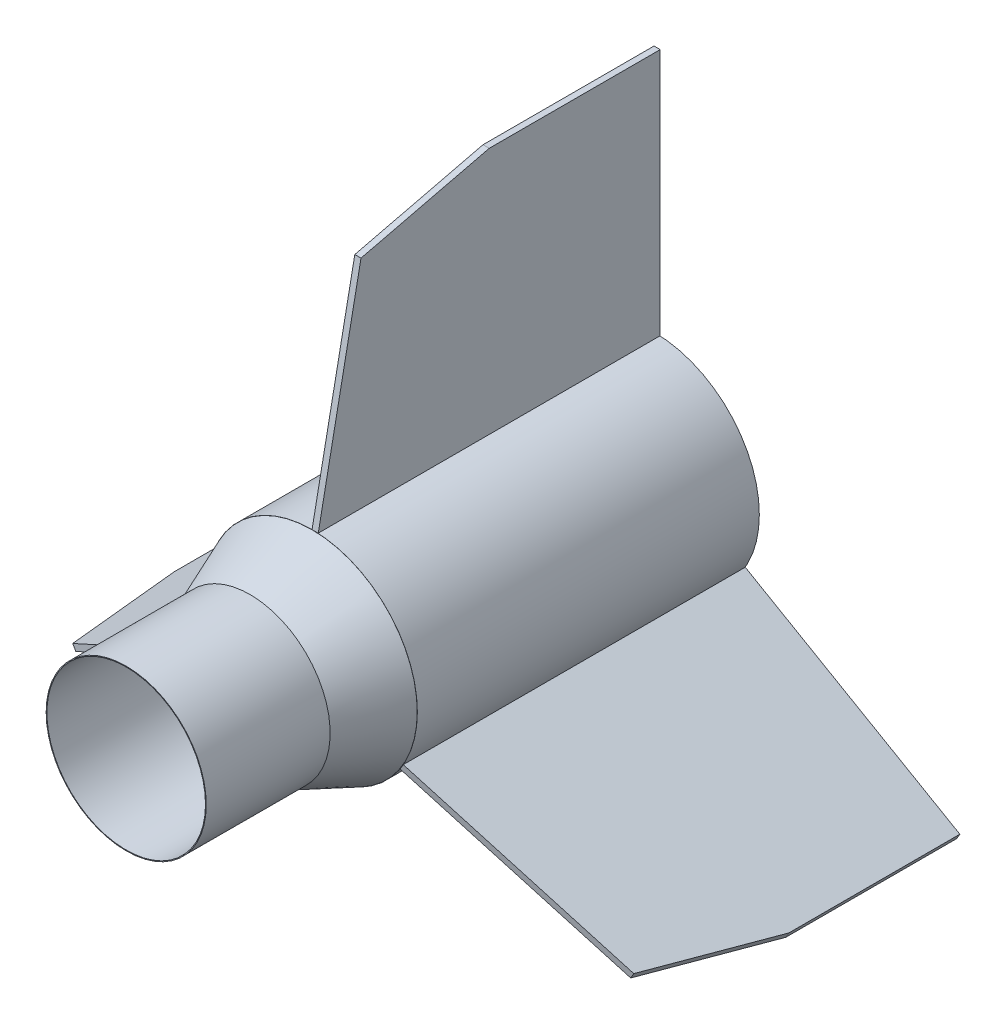
SolidWorks part; units mm, degrees
ref_plane "Front Plane" through (0, 0, 0) normal (0, 0, 1) x (1, 0, 0)
ref_plane "Top Plane" through (0, 0, 0) normal (0, 1, 0) x (1, 0, 0)
ref_plane "Right Plane" through (0, 0, 0) normal (1, 0, 0) x (0, 0, -1)
sketch "Sketch1" plane through (0, 0, 0) normal (0, 0, 1) x (1, 0, 0)
  line L0 (0, 0) -> (-20.1218, 11.3741) construction
  line L1 (0, 0) -> (19.9112, 11.7389) construction
  line L2 (0, 0) -> (0.2377, -23.114) construction
  circle A4 centre (0.1189, -11.557) radius 9.144
  circle A5 centre (9.9556, 5.8695) radius 9.144
  circle A6 centre (-10.0609, 5.687) radius 9.144
  circle A8 centre (0, 0) radius 21.59
  point P1 (2.188, 1.29)
  point P2 (-2.2112, 1.2499)
  point P6 (0.0261, -2.54)
  point P7 (9.9556, 5.8695)
  point P8 (-10.0609, 5.687)
  point P9 (0.1189, -11.557)
  dimension "D1" = 2.54
  dimension "D2" = 2.54
  dimension "D3" = 2.54
  dimension "D4" = 9.017
  dimension "D5" = 9.017
  dimension "D6" = 9.017
extrude "Boss-Extrude1" add sketch "Sketch1" along normal blind 70.1
sketch "Sketch2" plane through (0, 0, 70.1) normal (0, 0, 1) x (1, 0, 0)
  circle A0 centre (0, 0) radius 21.59
  circle A2 centre (0, 0) radius 16.4084
  circle A3 centre (0, 0) radius 16.256
  circle M4 centre (9.9556, 5.8695) radius 9.144
  circle M6 centre (0.1189, -11.557) radius 9.144
  circle M7 centre (-10.0609, 5.687) radius 9.144
extrude "Boss-Extrude2" add sketch "Sketch2" along normal blind 38.1 contours A3 A2 M7 | A3 A2 M4 M7 | A3 A2 M4 | A3 A2 M6 M4 | A3 A2 M6 | A3 A2 M7 M6
sketch "Sketch8" plane through (0, 0, 0) normal (1, 0, 0) x (0, 0, -1)
  line L0 (-126.1598, 0) -> (24.1508, 0) construction
  line L1 (-70.1, -0.6209) -> (-70.1, 31.6682) construction
  line L2 (-89.15, 16.4084) -> (-70.1, 16.4084) construction
  line L3 (-70.1, 16.4084) -> (-108.2, 16.4084) construction
  line L4 (-70.1, 21.5623) -> (-82.8, 16.4084)
  line L5 (-70.1, 21.5623) -> (-70.1, 16.4084)
  line L6 (-70.1, 16.4084) -> (-82.8, 16.4084)
  point P10 (-82.8, 16.4084)
  dimension "D1" = 12.7
revolve "Revolve3" add sketch "Sketch8" angle 360 about L0
sketch "Sketch14" plane through (0, 0, 0) normal (1, 0, 0) x (0, 0, -1)
  line L0 (-70.1, 21.59) -> (-61.3375, 66.04)
  line L3 (0, 21.59) -> (-70.1, 72.39) construction
  line L4 (0, 21.59) -> (-35.05, 72.39) construction
  line L5 (0, 21.59) -> (-70.1, 21.59) construction
  line L6 (-70.1, 21.59) -> (0, 72.39) construction
  line L7 (-61.3375, 66.04) -> (-35.05, 72.39)
  line L8 (-35.05, 72.39) -> (0, 72.39)
  line L9 (0, 72.39) -> (0, 46.99)
  line L10 (0, 46.99) -> (0, 21.59)
  line L11 (0, 21.59) -> (-70.1, 21.59)
  point P7 (-30.6688, 66.04)
  point P9 (-35.05, 46.99)
  point P10 (-57.4, 21.59)
  point P11 (-12.7, 21.59)
  point P12 (-70.1, 46.99)
  point P14 (0, 46.99)
  point P15 (-61.3375, 66.04)
  point P16 (-8.7625, 66.04)
  dimension "D3" = 12.7
  dimension "D1" = 6.35
  dimension "D2" = 50.8
  dimension "D4" = 12.7
extrude "Boss-Extrude6" add sketch "Sketch14" along normal blind 1.27 separate body
pattern_circular "CirPattern7" count 3 over 360 about axis through (0, 0, 0) along (0, 0, 1) of bodies 111
